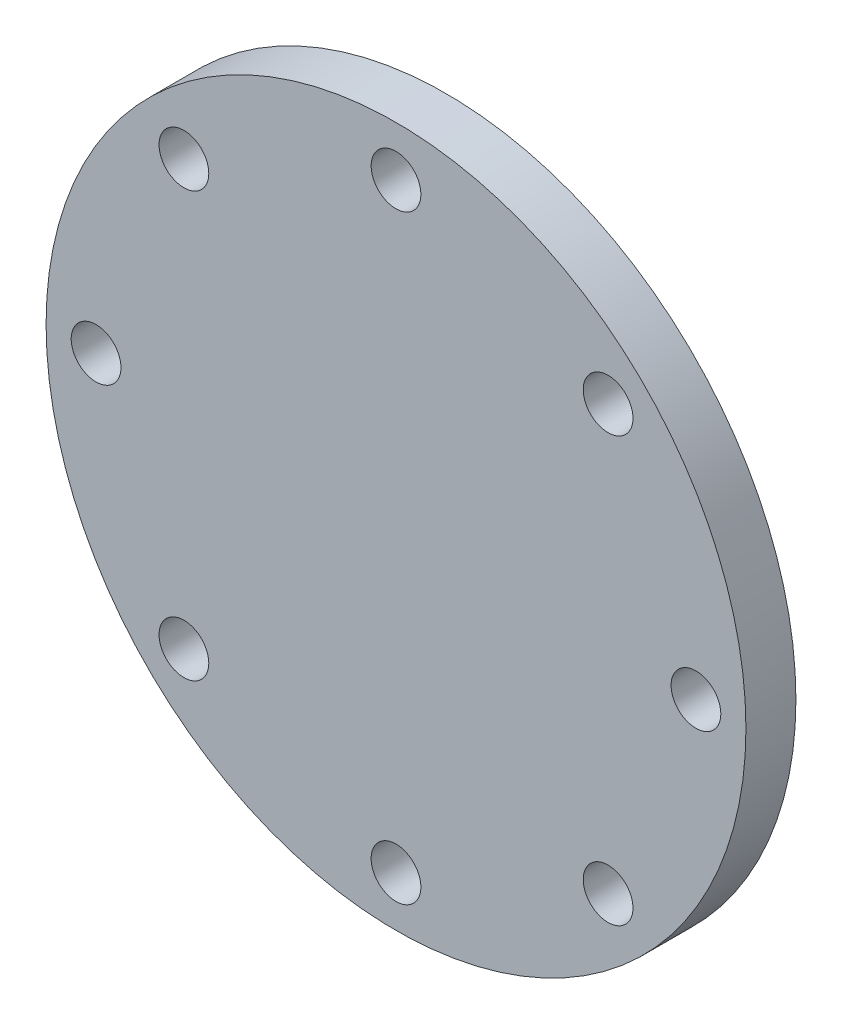
SolidWorks part; units mm, degrees
ref_plane "Front Plane" through (0, 0, 0) normal (0, 0, 1) x (1, 0, 0)
ref_plane "Top Plane" through (0, 0, 0) normal (0, 1, 0) x (1, 0, 0)
ref_plane "Right Plane" through (0, 0, 0) normal (1, 0, 0) x (0, 0, -1)
sketch "Sketch1" plane through (0, 0, 0) normal (0, 0, 1) x (1, 0, 0)
  circle A0 centre (0, 0) radius 17.78
extrude "Extrude1" add sketch "Sketch1" along normal blind 2.54
sketch "Sketch5" plane through (0, 0, 2.54) normal (0, 0, 1) x (1, 0, 0)
  line L0 (0, 17.78) -> (0, 15.24) construction
  circle A0 centre (0, 0) radius 17.78 construction
hole_wizard "#39 (0.0995) Diameter Hole2" positions "3DSketch3" profile "Sketch6" hole size "#39" standard "Ansi Inch"
sketch3d "3DSketch3"
  point P0 (0, 15.24, 2.54)
sketch "Sketch6" plane through (0, 15.24, 2.54) normal (1, 0, 0) x (0, -1, 0)
  line L0 (0, 0) -> (0, 10.9193)
  line L1 (0, 10.9193) -> (1.2636, 10.16)
  line L2 (1.2636, 10.16) -> (1.2636, 0)
  line L5 (1.2636, 0) -> (0, 0)
  line L10 (0, 10.9193) -> (-1.2636, 10.16) construction
  line L11 (0, -6.35) -> (0, 107.95) construction
  dimension "Hole Dia." = 2.5273
  dimension "Hole Depth" = 10.16
  dimension "Drill Angle" = 118
pattern_circular "CirPattern2" count 8 over 360 about axis through (0, 0, 0) along (0, 0, 1) of "#39 (0.0995) Diameter Hole2"
sketch "Sketch7" plane through (0, 0, 0) normal (0, 0, -1) x (-1, 0, 0)
  circle A0 centre (0, 0) radius 3.175
extrude "Extrude2" add sketch "Sketch7" along normal blind 2.54
